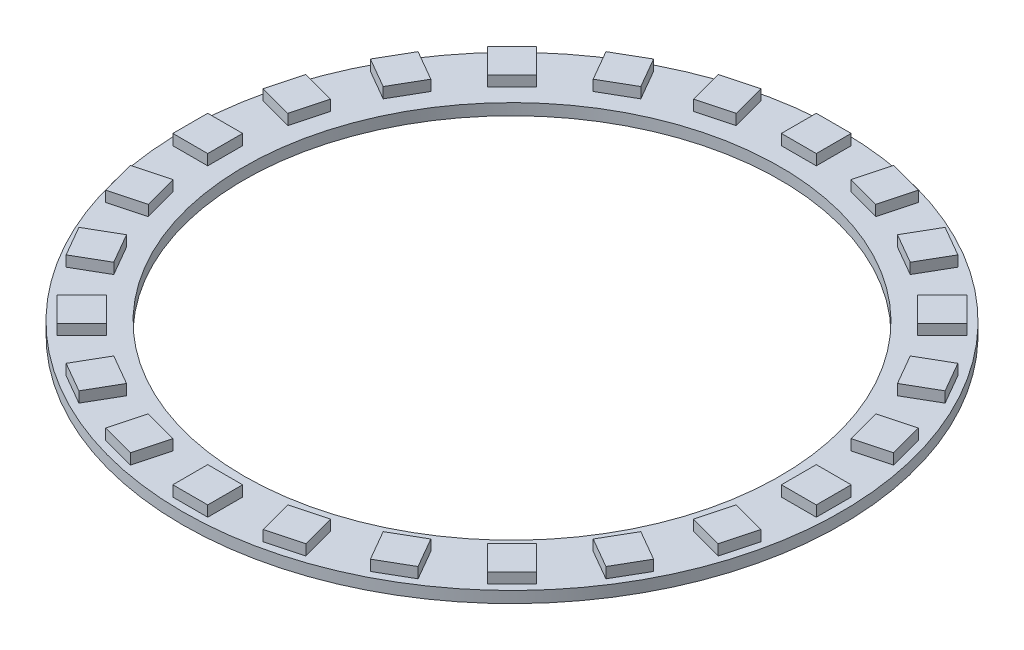
SolidWorks part; units mm, degrees
ref_plane "前视基准面" through (0, 0, 0) normal (0, 0, 1) x (1, 0, 0)
ref_plane "上视基准面" through (0, 0, 0) normal (0, 1, 0) x (1, 0, 0)
ref_plane "右视基准面" through (0, 0, 0) normal (1, 0, 0) x (0, 0, -1)
sketch "草图1" plane through (0, 0, 0) normal (0, 1, 0) x (1, 0, 0)
  circle A0 centre (0, 0) radius 46.3
  circle A1 centre (0, 0) radius 37.65
  dimension "D1" = 92.6
  dimension "D2" = 75.3
extrude "凸台-拉伸1" add sketch "草图1" along normal blind 1.6
sketch "草图2" plane through (0, 1.6, 0) normal (0, 1, 0) x (1, 0, 0)
  line L1 (-45.2, -2.45) -> (-40.3, -2.45)
  line L2 (-45.2, -2.45) -> (-45.2, 2.45)
  line L3 (-45.2, 2.45) -> (-40.3, 2.45)
  line L4 (-40.3, -2.45) -> (-40.3, 2.45)
  line L5 (-45.2, -2.45) -> (-40.3, 2.45) construction
  line L6 (-45.2, 2.45) -> (-40.3, -2.45) construction
  circle A0 centre (0, 0) radius 45.2 construction
  point P0 (-42.75, 0)
  point P7 (-20.8624, 0)
  dimension "D1" = 90.4
  dimension "D2" = 4.9
  dimension "D3" = 4.9
extrude "凸台-拉伸2" add sketch "草图2" along normal blind 1.5
pattern_circular "阵列(圆周)1" count 24 over 360 about axis through (0, 0, 0) along (0, 1, 0) of "凸台-拉伸2"
